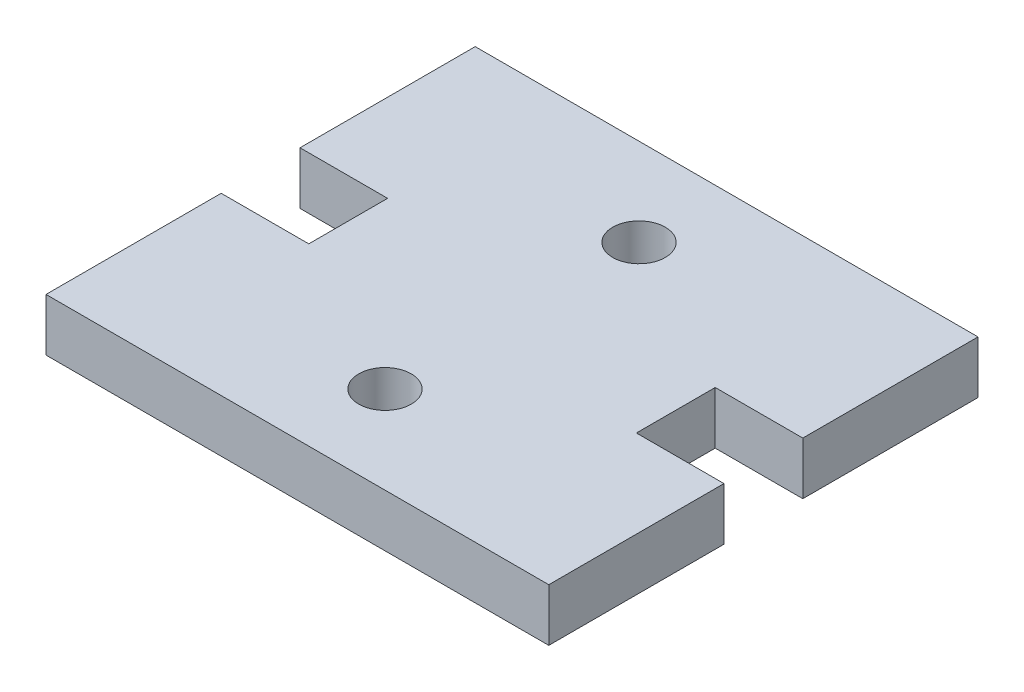
SolidWorks part; units mm, degrees
material "Teak"
ref_plane "Front Plane" through (0, 0, 0) normal (0, 0, 1) x (1, 0, 0)
ref_plane "Top Plane" through (0, 0, 0) normal (0, 1, 0) x (1, 0, 0)
ref_plane "Right Plane" through (0, 0, 0) normal (1, 0, 0) x (0, 0, -1)
sketch "Sketch1" plane through (0, 0, 0) normal (0, 1, 0) x (1, 0, 0)
  line L0 (-9.35, 2.25) -> (-9.35, -2.25) construction
  line L1 (-9.35, -2.25) -> (-14.35, -2.25) construction
  line L2 (-14.35, -2.25) -> (-14.35, -12.25) construction
  line L3 (-14.35, -12.25) -> (14.35, -12.25) construction
  line L4 (14.35, -12.25) -> (14.35, -2.25) construction
  line L5 (14.35, -2.25) -> (9.35, -2.25) construction
  line L6 (9.35, -2.25) -> (9.35, 2.25) construction
  line L7 (-9.35, 2.25) -> (-14.35, 2.25) construction
  line L8 (-14.35, 2.25) -> (-14.35, 12.25) construction
  line L9 (-14.35, 12.25) -> (14.35, 12.25) construction
  line L10 (14.35, 12.25) -> (14.35, 2.25) construction
  line L11 (14.35, 2.25) -> (9.35, 2.25) construction
  line L12 (-14.35, 2.25) -> (-14.35, 12.25)
  line L13 (-14.35, 12.25) -> (14.35, 12.25)
  line L14 (14.35, 12.25) -> (14.35, 2.25)
  line L15 (14.35, 2.25) -> (9.35, 2.25)
  line L16 (9.35, 2.25) -> (9.35, -2.25)
  line L17 (9.35, -2.25) -> (14.35, -2.25)
  line L18 (14.35, -2.25) -> (14.35, -12.25)
  line L19 (14.35, -12.25) -> (-14.35, -12.25)
  line L20 (-14.35, -12.25) -> (-14.35, -2.25)
  line L21 (-14.35, -2.25) -> (-9.35, -2.25)
  line L22 (-9.35, -2.25) -> (-9.35, 2.25)
  line L23 (-9.35, 2.25) -> (-14.35, 2.25)
  circle A0 centre (0, -7.25) radius 1.5 construction
  circle A1 centre (0, 7.25) radius 1.5 construction
  circle A2 centre (0, 7.25) radius 1.5
  circle A3 centre (0, -7.25) radius 1.5
extrude "Boss-Extrude1" add sketch "Sketch1" along normal blind 3
